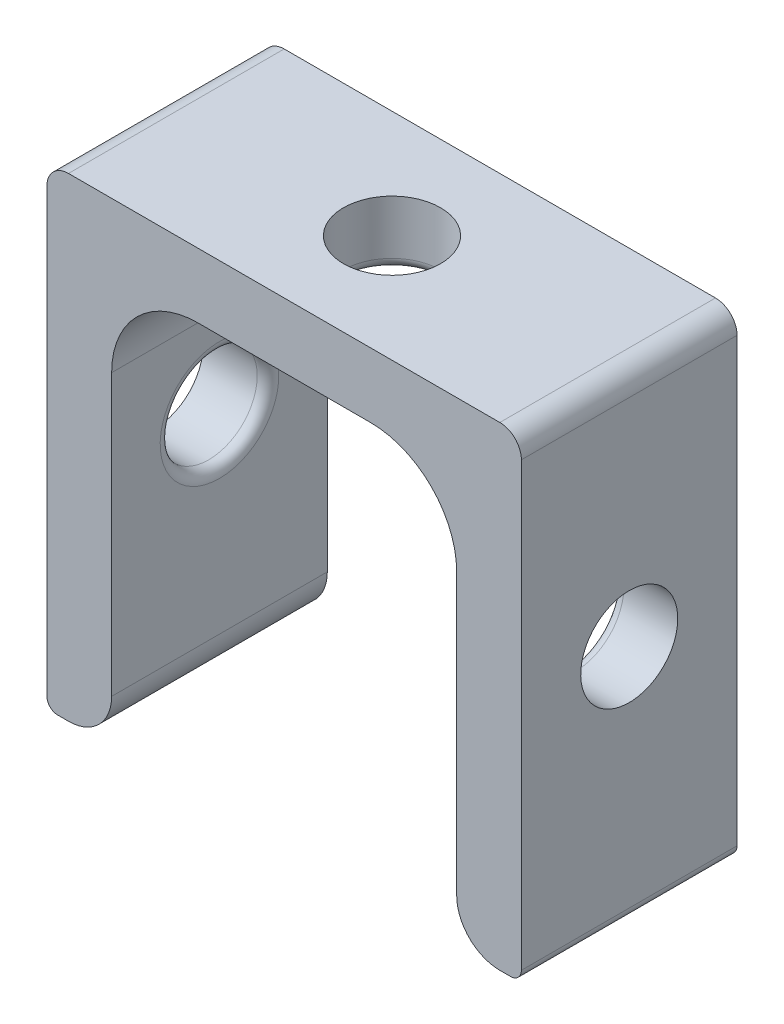
SolidWorks part; units mm, degrees
material "自定义塑料"
ref_plane "前视基准面" through (0, 0, 0) normal (0, 0, 1) x (1, 0, 0)
ref_plane "上视基准面" through (0, 0, 0) normal (0, 1, 0) x (1, 0, 0)
ref_plane "右视基准面" through (0, 0, 0) normal (1, 0, 0) x (0, 0, -1)
sketch "草图1" plane through (0, 0, 0) normal (0, 0, 1) x (1, 0, 0)
  line L1 (-8, 0) -> (-8, -17)
  line L2 (-10, -19) -> (-10.5, -19)
  line L3 (-11, -18.5) -> (-11, 3)
  line L5 (0, -5.5) -> (0, 5.5) construction
  line L9 (-11, 3) -> (11, 3)
  line L10 (-8, 0) -> (8, 0)
  line L11 (11, -18.5) -> (11, 3)
  line L12 (10, -19) -> (10.5, -19)
  line L13 (8, 0) -> (8, -17)
  arc A0 (-11, -18.5) -> (-10.5, -19) centre (-10.5, -18.5) ccw
  arc A1 (-8, -17) -> (-10, -19) centre (-10, -17) cw
  arc A2 (8, -17) -> (10, -19) centre (10, -17) ccw
  arc A3 (11, -18.5) -> (10.5, -19) centre (10.5, -18.5) cw
  point P12 (8, -19)
  point P15 (0, 0)
  point P17 (-11, -19)
  point P20 (-8, -19)
  point P23 (0, 0)
  point P24 (0, 3)
  point P25 (11, -19)
  dimension "D5" = 0.5
  dimension "D6" = 2
  dimension "D1" = 8
  dimension "D2" = 3
  dimension "D3" = 3
  dimension "D4" = 22
extrude "凸台-拉伸1" add sketch "草图1" along normal blind 10
sketch "草图2" plane through (11, 0, 0) normal (1, 0, 0) x (0, 0, -1)
  line L0 (0, -18.5) -> (0, 3) construction
  line L1 (-10, 3) -> (0, 3) construction
  circle A0 centre (-5, -8) radius 2.25
  dimension "D1" = 4.5
  dimension "D2" = 5
  dimension "D3" = 11
sketch "草图4" plane through (0, 0, 0) normal (0, 1, 0) x (1, 0, 0)
  line L0 (11, 0) -> (-11, 0) construction
  circle A0 centre (0, -5) radius 2.25
  dimension "D1" = 4.5
  dimension "D2" = 5
extrude "切除-拉伸1" cut sketch "草图4" along normal blind 10
extrude "切除-拉伸2" cut sketch "草图2" against normal blind 27
fillet "圆角2" radius 0.5 3 edges at (8, -5.75, 5) (-8, -10.25, 5) (0, 0, 7.25)
fillet "圆角3" radius 1 2 edges at (11, 3, 5) (-11, 3, 5)
fillet "圆角4" radius 4 2 edges at (8, 0, 5) (-8, 0, 5)
